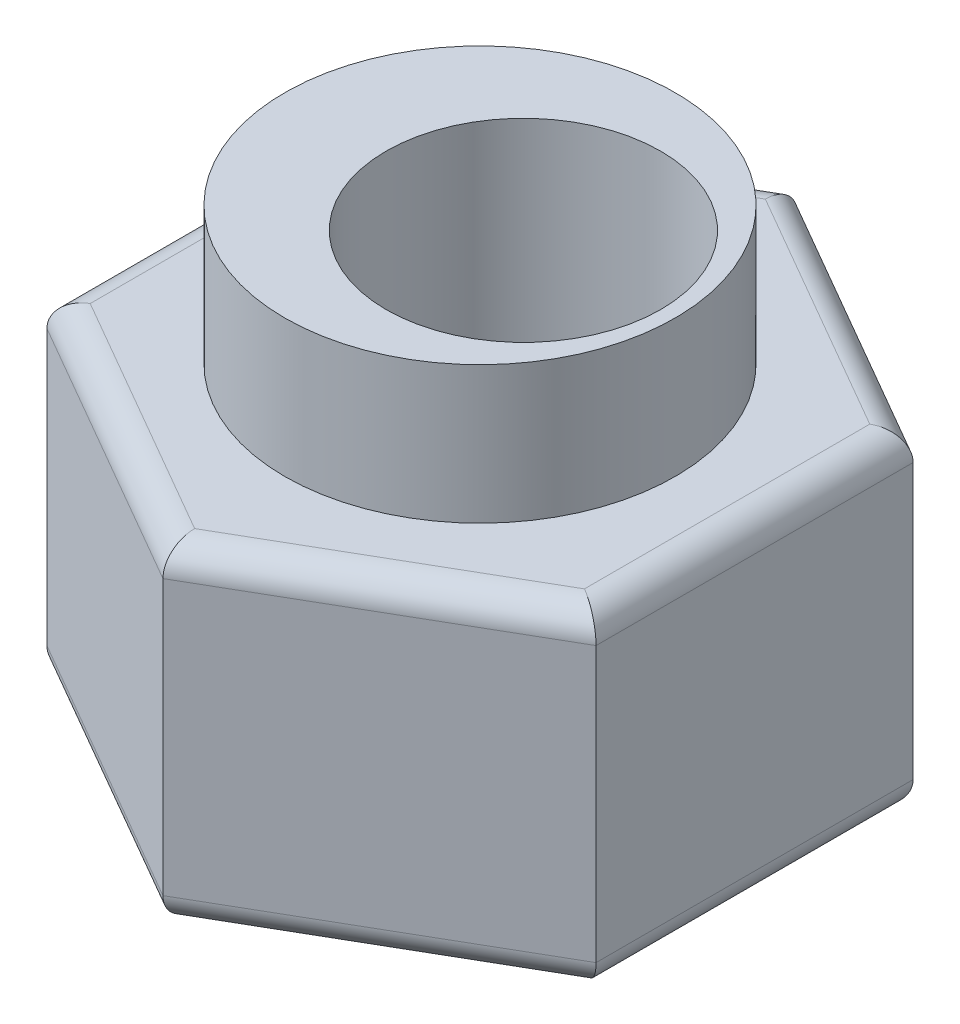
SolidWorks part; units mm, degrees
ref_plane "Front Plane" through (0, 0, 0) normal (0, 0, 1) x (1, 0, 0)
ref_plane "Top Plane" through (0, 0, 0) normal (0, 1, 0) x (1, 0, 0)
ref_plane "Right Plane" through (0, 0, 0) normal (1, 0, 0) x (0, 0, -1)
sketch "Sketch1" plane through (0, 0, 0) normal (0, 1, 0) x (1, 0, 0)
  line L1 (5, -2.8868) -> (5, 2.8868)
  line L2 (5, 2.8868) -> (0, 5.7735)
  line L3 (0, 5.7735) -> (-5, 2.8868)
  line L4 (-5, 2.8868) -> (-5, -2.8868)
  line L5 (-5, -2.8868) -> (0, -5.7735)
  line L6 (0, -5.7735) -> (5, -2.8868)
  circle A0 centre (0, 0) radius 5 construction
  dimension "D1" = 10
extrude "Boss-Extrude1" add sketch "Sketch1" along normal blind 6
sketch "Sketch2" plane through (0, 6, 0) normal (0, 1, 0) x (1, 0, 0)
  circle A0 centre (0, 0) radius 3.555
  dimension "D1" = 7.11
extrude "Boss-Extrude2" add sketch "Sketch2" along normal blind 2.5
sketch "Sketch3" plane through (0, 8.5, 0) normal (0, 1, 0) x (1, 0, 0)
  line L0 (0, 0) -> (3.555, 0) construction
  circle A0 centre (0, 0) radius 3.555 construction
  circle A1 centre (0.79, 0) radius 2.5
  dimension "D2" = 5
  dimension "D1" = 0.79
extrude "Cut-Extrude1" cut sketch "Sketch3" against normal through all
fillet "Fillet1" radius 0.5 12 edges at (5, 0, 0) (2.5, 0, -4.3301) (-2.5, 0, -4.3301) (-5, 0, 0) (-2.5, 0, 4.3301) (2.5, 0, 4.3301) (-5, 6, 0) (-2.5, 6, -4.3301) (2.5, 6, -4.3301) (5, 6, 0) (2.5, 6, 4.3301) (-2.5, 6, 4.3301)
